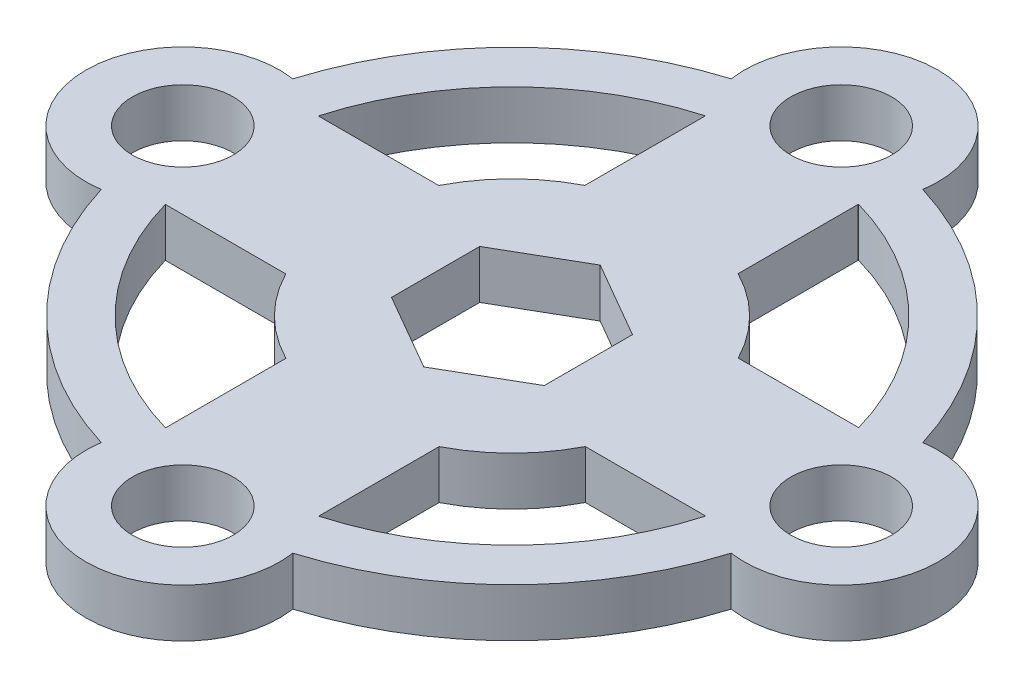
SolidWorks part; units mm, degrees
ref_plane "Front Plane" through (0, 0, 0) normal (0, 0, 1) x (1, 0, 0)
ref_plane "Top Plane" through (0, 0, 0) normal (0, 1, 0) x (1, 0, 0)
ref_plane "Right Plane" through (0, 0, 0) normal (1, 0, 0) x (0, 0, -1)
sketch "Sketch1" plane through (0, 0, 0) normal (0, 1, 0) x (1, 0, 0)
  line L0 (0, 0) -> (5, 0)
  line L1 (0, 5.7735) -> (-5, 2.8868)
  line L2 (-5, 2.8868) -> (-5, -2.8868)
  line L3 (-5, -2.8868) -> (0, -5.7735)
  line L4 (0, -5.7735) -> (5, -2.8868)
  line L5 (5, -2.8868) -> (5, 2.8868)
  line L6 (5, 2.8868) -> (0, 5.7735)
  line L7 (-5.0179, 17.6745) -> (-5.0179, 9.7888)
  line L8 (5, 17.6515) -> (5, 9.798)
  line L9 (17.6745, 5.0179) -> (9.7888, 5.0179)
  line L10 (17.6515, -5) -> (9.798, -5)
  line L11 (5.0179, -17.6745) -> (5.0179, -9.7888)
  line L12 (-5, -17.6515) -> (-5, -9.798)
  line L13 (-17.6745, -5.0179) -> (-9.7888, -5.0179)
  line L14 (-17.6515, 5) -> (-9.798, 5)
  circle A0 centre (0, 0) radius 11
  circle A1 centre (0, 0) radius 5 construction
  circle A2 centre (21.548, 0) radius 3.302
  circle A3 centre (21.548, 0) radius 6.339
  circle A4 centre (0, -21.548) radius 6.339
  circle A5 centre (0, -21.548) radius 3.302
  circle A6 centre (-21.548, 0) radius 6.339
  circle A7 centre (-21.548, 0) radius 3.302
  circle A8 centre (0, 21.548) radius 6.339
  circle A9 centre (0, 21.548) radius 3.302
  arc A10 (-6.2701, 20.6156) -> (-20.6156, 6.2701) centre (0, 0) ccw
  arc A11 (-17.6745, -5.0179) -> (-5.0179, -17.6745) centre (0, 0) ccw
  arc A12 (-20.6156, -6.2701) -> (-6.2701, -20.6156) centre (0, 0) ccw
  arc A13 (20.6156, 6.2701) -> (6.2701, 20.6156) centre (0, 0) ccw
  arc A14 (6.2701, -20.6156) -> (20.6156, -6.2701) centre (0, 0) ccw
  arc A15 (5.0179, -17.6745) -> (17.6745, -5.0179) centre (0, 0) ccw
  arc A16 (17.6745, 5.0179) -> (5.0179, 17.6745) centre (0, 0) ccw
  arc A17 (-5.0179, 17.6745) -> (-17.6745, 5.0179) centre (0, 0) ccw
  point P25 (0, 0)
  point P39 (12.9917, -12.9917)
  point P52 (0, 0)
  dimension "D1" = 21.548
  dimension "D2" = 6.604
  dimension "D3" = 4
  dimension "D5" = 12.678
  dimension "D6" = 21.548
  dimension "D4" = 4
extrude "Boss-Extrude1" add sketch "Sketch1" along normal blind 3.175 contours A17 A8 A10 A6 | A6 A7 | A6 A12 A4 A11 | A4 A5 | A6 L13 A0 L14 | A4 L11 A0 L12 | A0 L6 L5 L4 L3 L2 L1 | A8 L7 A0 L8 | A8 A9 | A16 A3 A13 A8 | A3 L9 A0 L10 | A3 A2 | A15 A4 A14 A3
